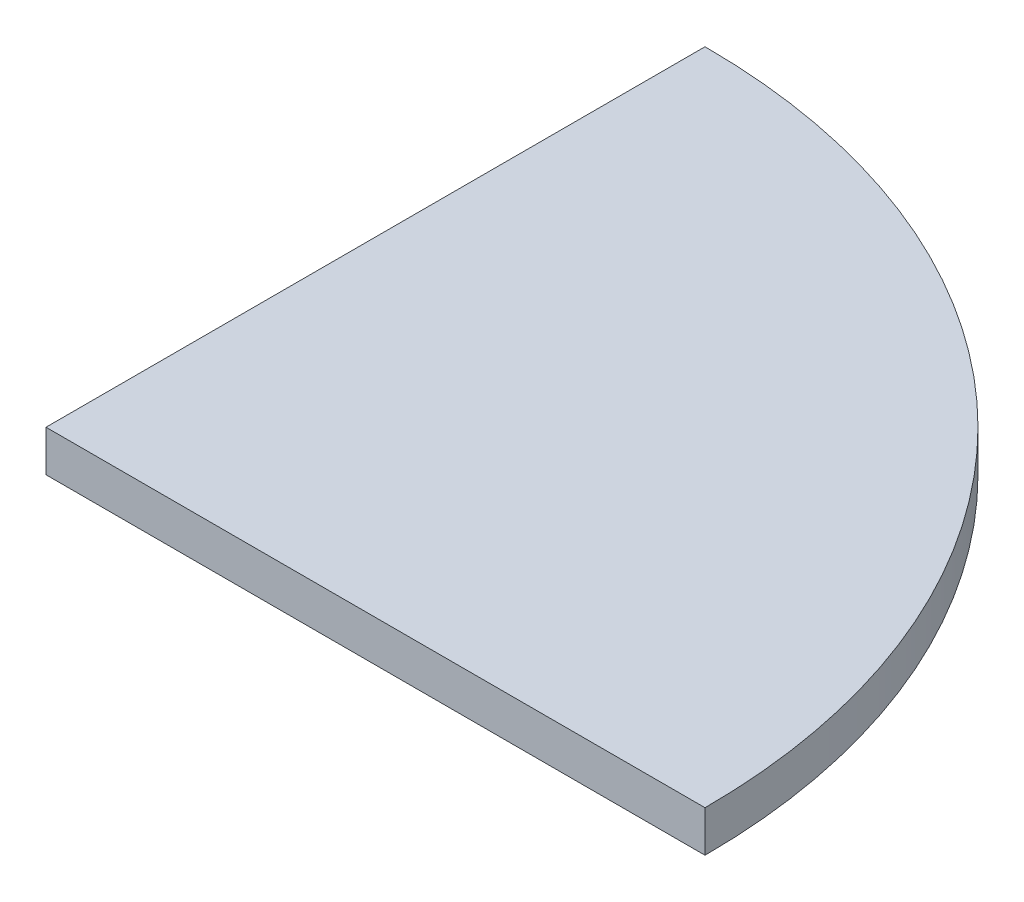
SolidWorks part; units mm, degrees
ref_plane "Front Plane" through (0, 0, 0) normal (0, 0, 1) x (1, 0, 0)
ref_plane "Top Plane" through (0, 0, 0) normal (0, 1, 0) x (1, 0, 0)
ref_plane "Right Plane" through (0, 0, 0) normal (1, 0, 0) x (0, 0, -1)
sketch "Sketch1" plane through (0, 0, 0) normal (0, 1, 0) x (1, 0, 0)
  line L0 (0, 304.8) -> (0, 0)
  line L1 (0, 0) -> (304.8, 0)
  arc A0 (304.8, 0) -> (0, 304.8) centre (0, 0) ccw
  dimension "D1" = 609.6
extrude "Boss-Extrude1" add sketch "Sketch1" along normal blind 19.05
